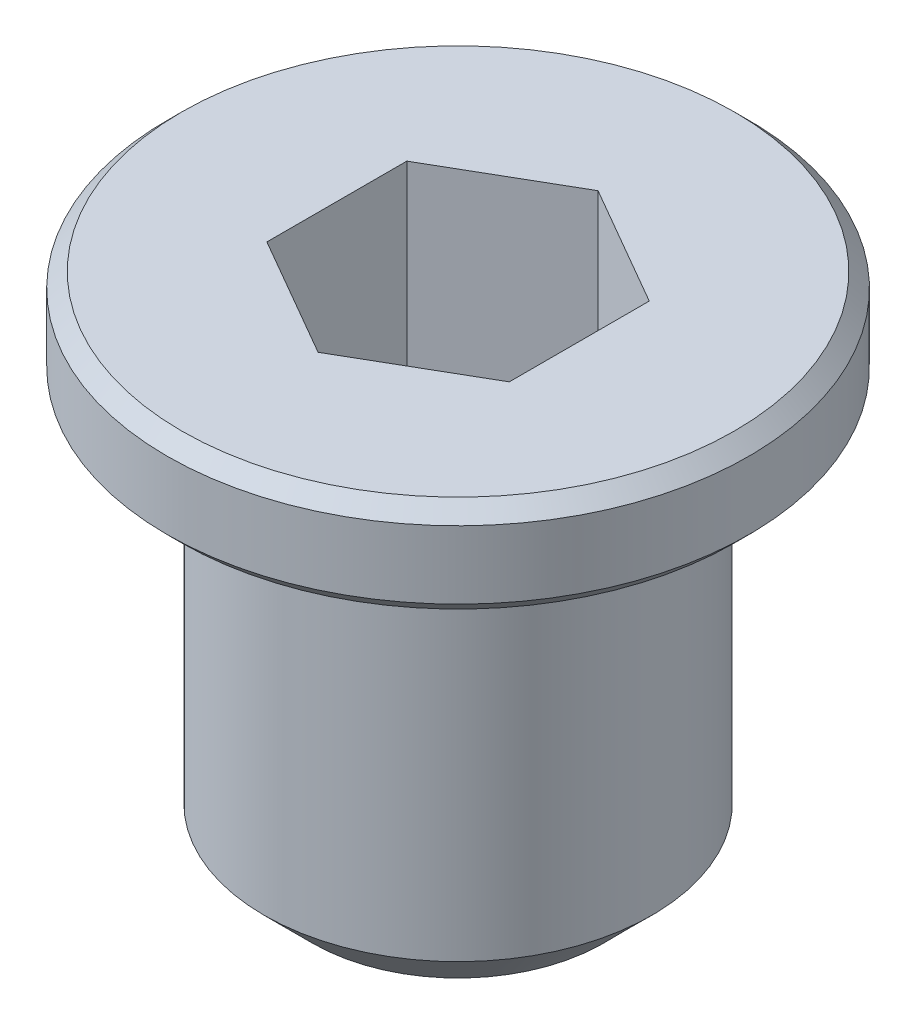
SolidWorks part; units mm, degrees
ref_plane "Plan de face" through (0, 0, 0) normal (0, 0, 1) x (1, 0, 0)
ref_plane "Plan de dessus" through (0, 0, 0) normal (0, 1, 0) x (1, 0, 0)
ref_plane "Plan de droite" through (0, 0, 0) normal (1, 0, 0) x (0, 0, -1)
sketch "Esquisse2" plane through (0, 0, 0) normal (0, 1, 0) x (1, 0, 0)
  circle A0 centre (0, 0) radius 4
  dimension "D1" = 8
extrude "Extrusion1" add sketch "Esquisse2" against normal blind 8.5
sketch "Esquisse3" plane through (0, 0, 0) normal (0, 1, 0) x (-1, 0, 0)
  circle A0 centre (0, 0) radius 6
  dimension "D1" = 12
extrude "Extrusion2" add sketch "Esquisse3" along normal blind 2
sketch "Esquisse4" plane through (0, 2, 0) normal (0, 1, 0) x (-1, 0, 0)
  circle A0 centre (0, 0) radius 2
  dimension "D1" = 4
extrude "Enlèv. mat.-Extru.1" cut sketch "Esquisse4" against normal through all
sketch "Esquisse5" plane through (0, 2, 0) normal (0, 1, 0) x (-1, 0, 0)
  line L1 (0, -2.8868) -> (2.5, -1.4434)
  line L2 (2.5, -1.4434) -> (2.5, 1.4434)
  line L3 (2.5, 1.4434) -> (0, 2.8868)
  line L4 (0, 2.8868) -> (-2.5, 1.4434)
  line L5 (-2.5, 1.4434) -> (-2.5, -1.4434)
  line L6 (-2.5, -1.4434) -> (0, -2.8868)
  circle A0 centre (0, 0) radius 2.5 construction
  dimension "D1" = 5
extrude "Enlèv. mat.-Extru.2" cut sketch "Esquisse5" against normal blind 5.5
chamfer "Chanfrein1" distance 0.3 angle 45 2 edges at (0, 0, 6) (0, 2, 6)
chamfer "Chanfrein2" distance 1 angle 45 1 edges at (0, -8.5, 4)
